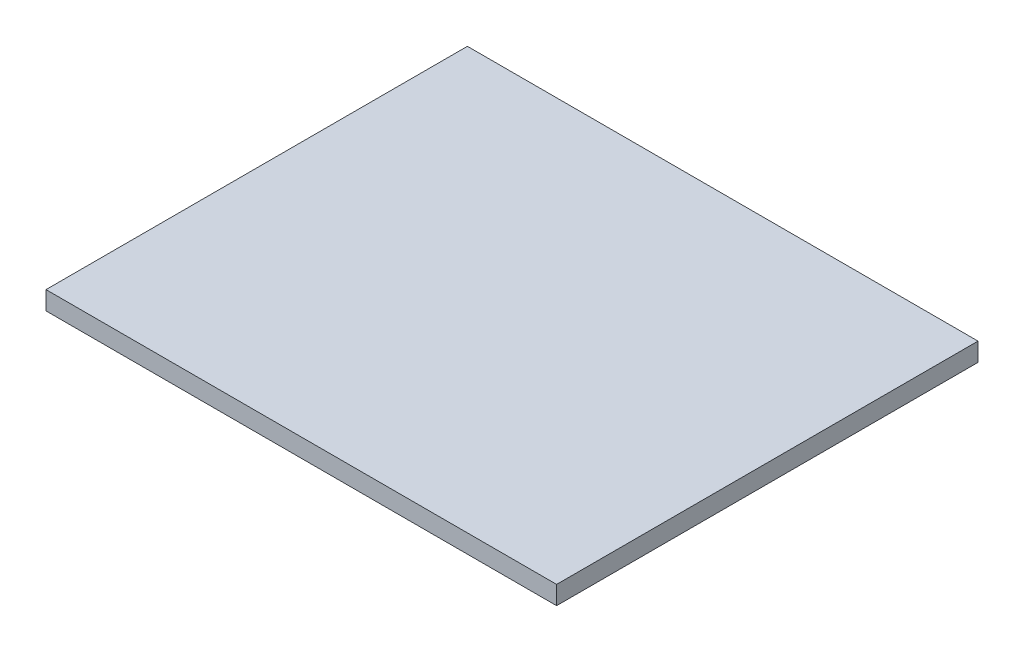
SolidWorks part; units mm, degrees
ref_plane "Front Plane" through (0, 0, 0) normal (0, 0, 1) x (1, 0, 0)
ref_plane "Top Plane" through (0, 0, 0) normal (0, 1, 0) x (1, 0, 0)
ref_plane "Right Plane" through (0, 0, 0) normal (1, 0, 0) x (0, 0, -1)
sketch "Sketch1" plane through (0, 0, 0) normal (0, 0, 1) x (1, 0, 0)
  line L0 (124.8, -220) -> (41.8, -220)
  line L1 (124.8, -220) -> (124.8, -223)
  line L2 (41.8, -220) -> (41.8, -223)
  line L3 (124.8, -223) -> (41.8, -223)
  line L4 (124.8, -98) -> (124.8, -350.4) construction
  line L5 (66, -220) -> (0, -220) construction
  dimension "D1" = 3
  dimension "D2" = 83
extrude "Boss-Extrude1" add sketch "Sketch1" along normal blind 68.5
